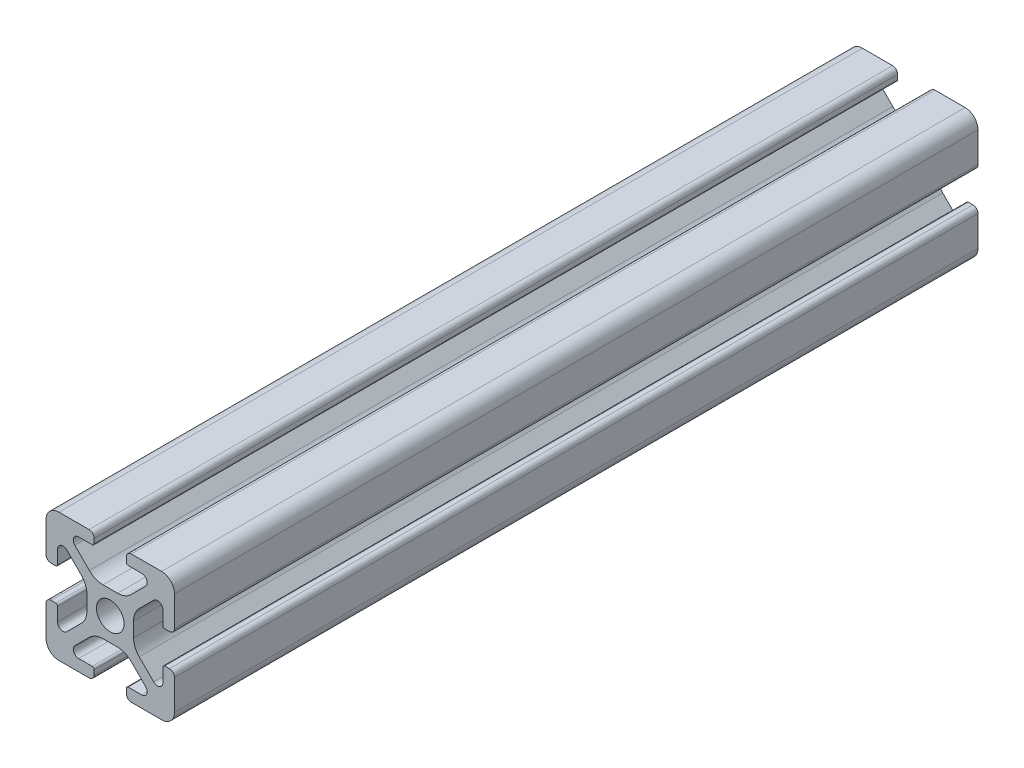
SolidWorks part; units mm, degrees
material "6061-T6 (SS)"
ref_plane "Front Plane" through (0, 0, 0) normal (0, 0, 1) x (1, 0, 0)
ref_plane "Top Plane" through (0, 0, 0) normal (0, 1, 0) x (1, 0, 0)
ref_plane "Right Plane" through (0, 0, 0) normal (1, 0, 0) x (0, 0, -1)
sketch "Sketch1" plane through (0, 0, 0) normal (0, 0, 1) x (1, 0, 0)
  line L2 (-9.9949, 7.9883) -> (-9.9949, 3.2893)
  line L3 (-7.9883, 9.9949) -> (-3.2893, 9.9949)
  line L4 (-2.5019, 9.2075) -> (-2.5019, 8.4963)
  line L5 (-2.8067, 8.1915) -> (-4.9149, 8.1915)
  line L6 (-5.5076, 6.7606) -> (-3.2528, 4.5058)
  line L7 (-6.7606, 5.5076) -> (-4.5058, 3.2528)
  line L8 (-8.1915, 4.9149) -> (-8.1915, 2.8067)
  line L9 (-8.4963, 2.5019) -> (-9.2075, 2.5019)
  line L11 (-1.1334, 3.6279) -> (1.1334, 3.6279)
  line L12 (-3.6279, 1.1334) -> (-3.6279, -1.1334)
  line L13 (8.4963, 2.5019) -> (9.2075, 2.5019)
  line L14 (8.1915, 4.9149) -> (8.1915, 2.8067)
  line L15 (9.9949, 7.9883) -> (9.9949, 3.2893)
  line L16 (7.9883, 9.9949) -> (3.2893, 9.9949)
  line L17 (2.5019, 9.2075) -> (2.5019, 8.4963)
  line L18 (2.8067, 8.1915) -> (4.9149, 8.1915)
  line L19 (3.6279, 1.1334) -> (3.6279, -1.1334)
  line L20 (5.5076, 6.7606) -> (3.2528, 4.5058)
  line L21 (6.7606, 5.5076) -> (4.5058, 3.2528)
  line L22 (-8.4963, -2.5019) -> (-9.2075, -2.5019)
  line L23 (-8.1915, -4.9149) -> (-8.1915, -2.8067)
  line L24 (-6.7606, -5.5076) -> (-4.5058, -3.2528)
  line L25 (-5.5076, -6.7606) -> (-3.2528, -4.5058)
  line L26 (-2.8067, -8.1915) -> (-4.9149, -8.1915)
  line L27 (-2.5019, -9.2075) -> (-2.5019, -8.4963)
  line L28 (-7.9883, -9.9949) -> (-3.2893, -9.9949)
  line L29 (-9.9949, -7.9883) -> (-9.9949, -3.2893)
  line L30 (9.9949, -7.9883) -> (9.9949, -3.2893)
  line L31 (7.9883, -9.9949) -> (3.2893, -9.9949)
  line L32 (2.5019, -9.2075) -> (2.5019, -8.4963)
  line L33 (2.8067, -8.1915) -> (4.9149, -8.1915)
  line L34 (5.5076, -6.7606) -> (3.2528, -4.5058)
  line L35 (6.7606, -5.5076) -> (4.5058, -3.2528)
  line L36 (8.1915, -4.9149) -> (8.1915, -2.8067)
  line L37 (8.4963, -2.5019) -> (9.2075, -2.5019)
  line L38 (-1.1334, -3.6279) -> (1.1334, -3.6279)
  circle A0 centre (0, 0) radius 2.1463
  arc A1 (-9.9949, 7.9883) -> (-7.9883, 9.9949) centre (-7.9883, 7.9883) cw
  arc A2 (-6.7606, 5.5076) -> (-8.1915, 4.9149) centre (-7.3533, 4.9149) ccw
  arc A3 (-4.9149, 8.1915) -> (-5.5076, 6.7606) centre (-4.9149, 7.3533) ccw
  arc A4 (-3.2893, 9.9949) -> (-2.5019, 9.2075) centre (-3.2893, 9.2075) cw
  arc A5 (-9.9949, 3.2893) -> (-9.2075, 2.5019) centre (-9.2075, 3.2893) ccw
  arc A6 (-8.1915, 2.8067) -> (-8.4963, 2.5019) centre (-8.4963, 2.8067) cw
  arc A7 (-2.5019, 8.4963) -> (-2.8067, 8.1915) centre (-2.8067, 8.4963) cw
  arc A8 (-1.1334, 3.6279) -> (-3.2528, 4.5058) centre (-1.1334, 6.6251) cw
  arc A9 (-3.6279, 1.1334) -> (-4.5058, 3.2528) centre (-6.6251, 1.1334) ccw
  arc A10 (8.1915, 2.8067) -> (8.4963, 2.5019) centre (8.4963, 2.8067) ccw
  arc A11 (9.9949, 3.2893) -> (9.2075, 2.5019) centre (9.2075, 3.2893) cw
  arc A12 (9.9949, 7.9883) -> (7.9883, 9.9949) centre (7.9883, 7.9883) ccw
  arc A13 (3.2893, 9.9949) -> (2.5019, 9.2075) centre (3.2893, 9.2075) ccw
  arc A14 (2.5019, 8.4963) -> (2.8067, 8.1915) centre (2.8067, 8.4963) ccw
  arc A15 (1.1334, 3.6279) -> (3.2528, 4.5058) centre (1.1334, 6.6251) ccw
  arc A16 (3.6279, 1.1334) -> (4.5058, 3.2528) centre (6.6251, 1.1334) cw
  arc A17 (6.7606, 5.5076) -> (8.1915, 4.9149) centre (7.3533, 4.9149) cw
  arc A18 (4.9149, 8.1915) -> (5.5076, 6.7606) centre (4.9149, 7.3533) cw
  arc A19 (-3.6279, -1.1334) -> (-4.5058, -3.2528) centre (-6.6251, -1.1334) cw
  arc A20 (-1.1334, -3.6279) -> (-3.2528, -4.5058) centre (-1.1334, -6.6251) ccw
  arc A21 (-2.5019, -8.4963) -> (-2.8067, -8.1915) centre (-2.8067, -8.4963) ccw
  arc A22 (-8.1915, -2.8067) -> (-8.4963, -2.5019) centre (-8.4963, -2.8067) ccw
  arc A23 (-9.9949, -3.2893) -> (-9.2075, -2.5019) centre (-9.2075, -3.2893) cw
  arc A24 (-3.2893, -9.9949) -> (-2.5019, -9.2075) centre (-3.2893, -9.2075) ccw
  arc A25 (-4.9149, -8.1915) -> (-5.5076, -6.7606) centre (-4.9149, -7.3533) cw
  arc A26 (-6.7606, -5.5076) -> (-8.1915, -4.9149) centre (-7.3533, -4.9149) cw
  arc A27 (-9.9949, -7.9883) -> (-7.9883, -9.9949) centre (-7.9883, -7.9883) ccw
  arc A28 (9.9949, -7.9883) -> (7.9883, -9.9949) centre (7.9883, -7.9883) cw
  arc A29 (6.7606, -5.5076) -> (8.1915, -4.9149) centre (7.3533, -4.9149) ccw
  arc A30 (4.9149, -8.1915) -> (5.5076, -6.7606) centre (4.9149, -7.3533) ccw
  arc A31 (3.2893, -9.9949) -> (2.5019, -9.2075) centre (3.2893, -9.2075) cw
  arc A32 (9.9949, -3.2893) -> (9.2075, -2.5019) centre (9.2075, -3.2893) ccw
  arc A33 (8.1915, -2.8067) -> (8.4963, -2.5019) centre (8.4963, -2.8067) cw
  arc A34 (2.5019, -8.4963) -> (2.8067, -8.1915) centre (2.8067, -8.4963) cw
  arc A35 (1.1334, -3.6279) -> (3.2528, -4.5058) centre (1.1334, -6.6251) cw
  arc A36 (3.6279, -1.1334) -> (4.5058, -3.2528) centre (6.6251, -1.1334) ccw
extrude "Boss-Extrude1" add sketch "Sketch1" along normal mid plane 125
